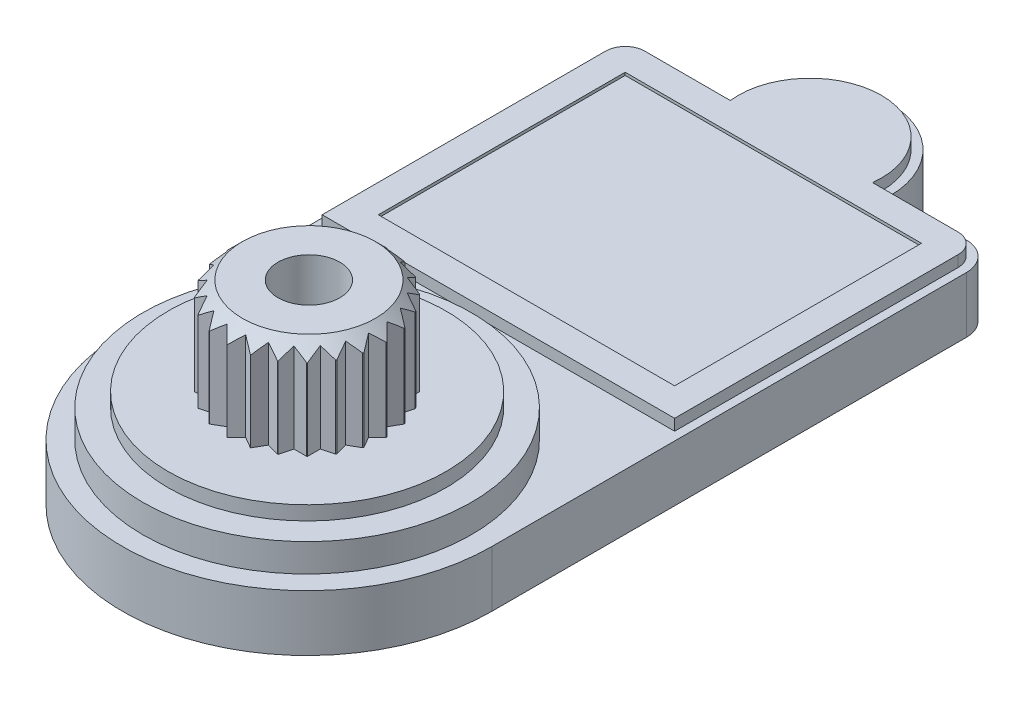
SolidWorks part; units mm, degrees
ref_plane "Front Plane" through (0, 0, 0) normal (0, 0, 1) x (1, 0, 0)
ref_plane "Top Plane" through (0, 0, 0) normal (0, 1, 0) x (1, 0, 0)
ref_plane "Right Plane" through (0, 0, 0) normal (1, 0, 0) x (0, 0, -1)
sketch "Sketch1" plane through (0, 0, 0) normal (0, 1, 0) x (1, 0, 0)
  line L0 (-6.575, 10) -> (6.575, 10)
  line L1 (5.575, -14.5) -> (-5.575, -14.5)
  line L2 (6.575, -13.5) -> (6.575, 13.5)
  line L3 (5.575, 14.5) -> (-5.575, 14.5)
  line L4 (-6.575, -13.5) -> (-6.575, 13.5)
  line L5 (6.575, -14.5) -> (-6.575, 14.5) construction
  line L6 (6.575, 14.5) -> (-6.575, -14.5) construction
  arc A0 (-6.575, -13.5) -> (-5.575, -14.5) centre (-5.575, -13.5) ccw
  arc A1 (5.575, -14.5) -> (6.575, -13.5) centre (5.575, -13.5) ccw
  arc A2 (6.575, 13.5) -> (5.575, 14.5) centre (5.575, 13.5) ccw
  arc A3 (-5.575, 14.5) -> (-6.575, 13.5) centre (-5.575, 13.5) ccw
  circle A4 centre (0, -7.9) radius 6.575
  circle A5 centre (0, 10) radius 2.85
  circle A6 centre (-5.575, 9) radius 1
  circle A7 centre (5.575, 9) radius 1
  point P2 (0, 0)
  dimension "D3" = 1
  dimension "D5" = 4.5
  dimension "D6" = 5.7
  dimension "D1" = 13.15
  dimension "D2" = 29
  dimension "D4" = 6.6
extrude "Boss-Extrude1" add sketch "Sketch1" along normal blind 2 contours A4 | A7 L0 A5 A6 L4 A4 L2 | A6 | L0 A5 | L0 A5 | A7
sketch "Sketch2" plane through (0, 2, 0) normal (0, 1, 0) x (-1, 0, 0)
  circle A0 centre (0, 7.9) radius 5.85
  dimension "D1" = 11.7
extrude "Boss-Extrude2" add sketch "Sketch2" along normal blind 1
sketch "Sketch3" plane through (0, 3, 0) normal (0, 1, 0) x (-1, 0, 0)
  circle A0 centre (0, 7.9) radius 4.95
  dimension "D1" = 9.9
extrude "Boss-Extrude3" add sketch "Sketch3" along normal blind 0.5
sketch "Sketch4" plane through (0, 3.5, 0) normal (0, 1, 0) x (-1, 0, 0)
  line L0 (0, 10.75) -> (0, 10.1208)
  line L1 (0, 10.75) -> (-0.7689, 10.6443)
  line L2 (-0.7689, 10.6443) -> (-1.4808, 10.3351)
  line L3 (-1.4808, 10.3351) -> (-2.0829, 9.8453)
  line L4 (-2.0829, 9.8453) -> (-2.5305, 9.2112)
  line L5 (-2.5305, 9.2112) -> (-2.7904, 8.4798)
  line L6 (-2.7904, 8.4798) -> (-2.8434, 7.7055)
  line L7 (-2.8434, 7.7055) -> (-2.6854, 6.9456)
  line L8 (-2.6854, 6.9456) -> (-2.3284, 6.2565)
  line L9 (-2.3284, 6.2565) -> (-1.7986, 5.6892)
  line L10 (-1.7986, 5.6892) -> (-1.1354, 5.2859)
  line L11 (-1.1354, 5.2859) -> (-0.3881, 5.0765)
  line L12 (-0.3881, 5.0765) -> (0.3881, 5.0765)
  line L13 (0.3881, 5.0765) -> (1.1354, 5.2859)
  line L14 (1.1354, 5.2859) -> (1.7986, 5.6892)
  line L15 (1.7986, 5.6892) -> (2.3284, 6.2565)
  line L16 (2.3284, 6.2565) -> (2.6854, 6.9456)
  line L17 (2.6854, 6.9456) -> (2.8434, 7.7055)
  line L18 (2.8434, 7.7055) -> (2.7904, 8.4798)
  line L19 (2.7904, 8.4798) -> (2.5305, 9.2112)
  line L20 (2.5305, 9.2112) -> (2.0829, 9.8453)
  line L21 (2.0829, 9.8453) -> (1.4808, 10.3351)
  line L22 (1.4808, 10.3351) -> (0.7689, 10.6443)
  line L23 (0.7689, 10.6443) -> (0, 10.75)
  line L24 (0, 10.75) -> (0.5653, 10.1847)
  line L25 (0, 10.75) -> (-0.5653, 10.1847)
  line L26 (0.7376, 10.6529) -> (0.0453, 10.2532)
  line L27 (0.7376, 10.6529) -> (1.1374, 9.9605)
  line L28 (1.425, 10.3682) -> (0.6528, 10.1613)
  line L29 (1.425, 10.3682) -> (1.6319, 9.596)
  line L30 (2.0153, 9.9153) -> (1.2158, 9.9153)
  line L31 (2.0153, 9.9153) -> (2.0153, 9.1158)
  line L32 (2.4682, 9.325) -> (1.696, 9.5319)
  line L33 (2.4682, 9.325) -> (2.2613, 8.5528)
  line L34 (2.7529, 8.6376) -> (2.0605, 9.0374)
  line L35 (2.7529, 8.6376) -> (2.3532, 7.9453)
  line L36 (2.85, 7.9) -> (2.2847, 8.4653)
  line L37 (2.85, 7.9) -> (2.2847, 7.3347)
  line L38 (2.7529, 7.1624) -> (2.3532, 7.8547)
  line L39 (2.7529, 7.1624) -> (2.0605, 6.7626)
  line L40 (2.4682, 6.475) -> (2.2613, 7.2472)
  line L41 (2.4682, 6.475) -> (1.696, 6.2681)
  line L42 (2.0153, 5.8847) -> (2.0153, 6.6842)
  line L43 (2.0153, 5.8847) -> (1.2158, 5.8847)
  line L44 (1.425, 5.4318) -> (1.6319, 6.204)
  line L45 (1.425, 5.4318) -> (0.6528, 5.6387)
  line L46 (0.7376, 5.1471) -> (1.1374, 5.8395)
  line L47 (0.7376, 5.1471) -> (0.0453, 5.5468)
  line L48 (0, 5.05) -> (0.5653, 5.6153)
  line L49 (0, 5.05) -> (-0.5653, 5.6153)
  line L50 (-0.7376, 5.1471) -> (-0.0453, 5.5468)
  line L51 (-0.7376, 5.1471) -> (-1.1374, 5.8395)
  line L52 (-1.425, 5.4318) -> (-0.6528, 5.6387)
  line L53 (-1.425, 5.4318) -> (-1.6319, 6.204)
  line L54 (-2.0153, 5.8847) -> (-1.2158, 5.8847)
  line L55 (-2.0153, 5.8847) -> (-2.0153, 6.6842)
  line L56 (-2.4682, 6.475) -> (-1.696, 6.2681)
  line L57 (-2.4682, 6.475) -> (-2.2613, 7.2472)
  line L58 (-2.7529, 7.1624) -> (-2.0605, 6.7626)
  line L59 (-2.7529, 7.1624) -> (-2.3532, 7.8547)
  line L60 (-2.85, 7.9) -> (-2.2847, 7.3347)
  line L61 (-2.85, 7.9) -> (-2.2847, 8.4653)
  line L62 (-2.7529, 8.6376) -> (-2.3532, 7.9453)
  line L63 (-2.7529, 8.6376) -> (-2.0605, 9.0374)
  line L64 (-2.4682, 9.325) -> (-2.2613, 8.5528)
  line L65 (-2.4682, 9.325) -> (-1.696, 9.5319)
  line L66 (-2.0153, 9.9153) -> (-2.0153, 9.1158)
  line L67 (-2.0153, 9.9153) -> (-1.2158, 9.9153)
  line L68 (-1.425, 10.3682) -> (-1.6319, 9.596)
  line L69 (-1.425, 10.3682) -> (-0.6528, 10.1613)
  line L70 (-0.7376, 10.6529) -> (-1.1374, 9.9605)
  line L71 (-0.7376, 10.6529) -> (-0.0453, 10.2532)
  circle A0 centre (0, 7.9) radius 2.85
  circle A1 centre (0, 7.9) radius 2.85 construction
  circle A2 centre (0, 7.9) radius 2.5
  dimension "D1" = 5.7
  dimension "D3" = 5
  dimension "D2" = 45
  dimension "D4" = 24
extrude "Boss-Extrude4" add sketch "Sketch4" along normal blind 3.4
sketch "Sketch5" plane through (0, 0, 0) normal (1, 0, 0) x (0, 0, -1)
  line L0 (-5.8672, 7.3) -> (-4.5172, 7.3)
  line L1 (-5.8672, 7.3) -> (-4.5172, 5.95)
  line L2 (-4.5172, 7.3) -> (-4.5172, 5.95)
  line L3 (-5.4679, 6.9) -> (-5.8847, 6.9) construction
  line L4 (-7.8361, 8.0778) -> (-7.8361, 5.141) construction
  dimension "D1" = 45
  dimension "D2" = 0.4
revolve "Cut-Revolve1" cut sketch "Sketch5" angle 360 about L4
sketch "Sketch6" plane through (0, 6.9, 0) normal (0, 1, 0) x (-1, 0, 0)
  circle A0 centre (0, 7.8361) radius 1.1
  dimension "D1" = 2.2
extrude "Cut-Extrude1" cut sketch "Sketch6" against normal blind 4
sketch "Sketch7" plane through (0, 2, 0) normal (0, 1, 0) x (-1, 0, 0)
  line L0 (-6.575, -1.6546) -> (-6.575, -9)
  line L1 (-6.575, 7.9) -> (-6.575, -9) construction
  line L2 (-5.575, -10) -> (-2.85, -10)
  line L3 (6.275, -9) -> (6.275, 1.0902)
  line L4 (2.85, -10) -> (5.575, -10)
  line L5 (5.575, -10) -> (6.575, -9)
  line L6 (6.575, -9) -> (6.575, 1.3902)
  line L7 (6.575, 7.9) -> (6.575, -9) construction
  line L8 (6.575, 1.3902) -> (-6.575, 1.3902)
  line L9 (-6.575, 1.3902) -> (-6.575, -1.6546)
  line L10 (6.275, 1.0902) -> (-6.275, 1.0902)
  line L11 (-6.275, 1.0902) -> (-6.275, -1.6546)
  line L12 (-6.275, -1.6546) -> (-6.275, -9)
  line L13 (-5.575, -9.7) -> (-2.5323, -9.7)
  line L14 (2.5323, -9.7) -> (5.575, -9.7)
  arc A0 (-2.85, -10) -> (2.85, -10) centre (0, -10) ccw
  arc A1 (-6.575, -9) -> (-5.575, -10) centre (-5.575, -9) ccw
  arc A2 (5.575, -10) -> (6.575, -9) centre (5.575, -9) ccw
  arc A3 (-6.275, -9) -> (-5.575, -9.7) centre (-5.575, -9) ccw
  arc A4 (-2.5323, -9.7) -> (2.5323, -9.7) centre (0, -10) ccw
  arc A5 (5.575, -9.7) -> (6.275, -9) centre (5.575, -9) ccw
  dimension "D1" = 0.3
extrude "Boss-Extrude5" add sketch "Sketch7" along normal blind 0.4 contours L14 A5 L3 L10 L11 L12 A3 L13 A4
sketch "Sketch8" plane through (0, 2.4, 0) normal (0, 1, 0) x (-1, 0, 0)
  line L0 (-6.275, 1.0902) -> (-6.275, -9) construction
  line L1 (-5.275, 0.0902) -> (5.275, 0.0902)
  line L2 (-5.275, 0.0902) -> (-5.275, -8.7)
  line L3 (-5.275, -8.7) -> (5.275, -8.7)
  line L4 (5.275, 0.0902) -> (5.275, -8.7)
  line L5 (6.275, 1.0902) -> (-6.275, 1.0902) construction
  line L6 (6.275, -9) -> (6.275, 1.0902) construction
  line L7 (2.5323, -9.7) -> (5.575, -9.7) construction
  dimension "D1" = 1
  dimension "D2" = 1
  dimension "D3" = 1
  dimension "D4" = 1
extrude "Cut-Extrude2" cut sketch "Sketch8" against normal blind 0.1
